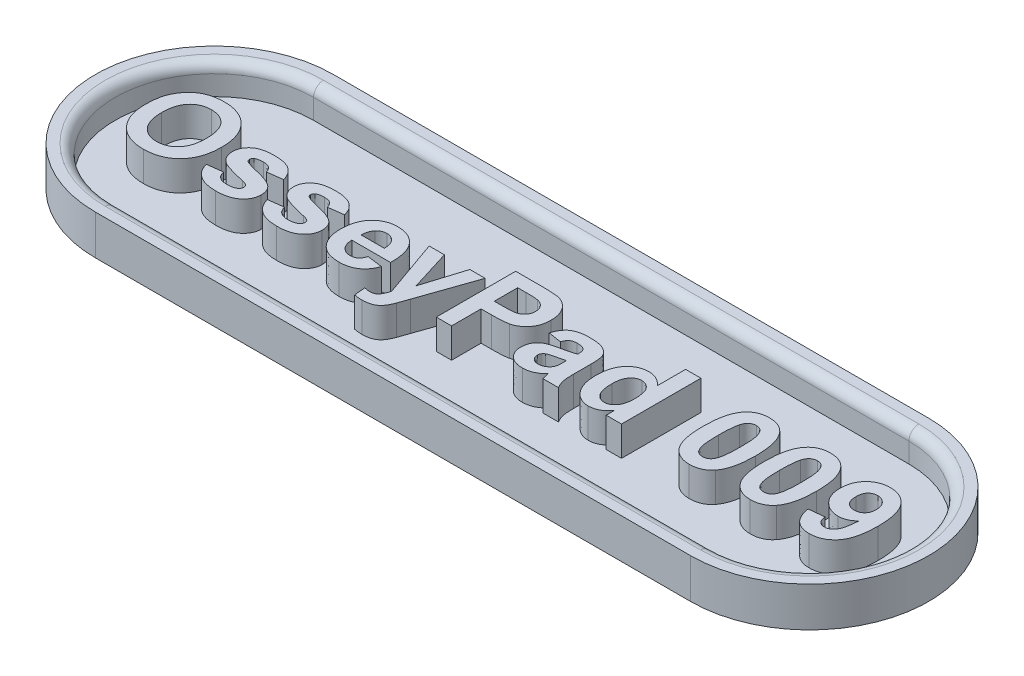
SolidWorks part; units mm, degrees
ref_plane "Front Plane" through (0, 0, 0) normal (0, 0, 1) x (1, 0, 0)
ref_plane "Top Plane" through (0, 0, 0) normal (0, 1, 0) x (1, 0, 0)
ref_plane "Right Plane" through (0, 0, 0) normal (1, 0, 0) x (0, 0, -1)
sketch "Sketch1" plane through (0, 0, 0) normal (0, 1, 0) x (1, 0, 0)
  line L0 (-15, 0) -> (15, 0) construction
  line L1 (-15, 6) -> (15, 6)
  line L2 (-15, -6) -> (15, -6)
  arc A0 (-15, 6) -> (-15, -6) centre (-15, 0) ccw
  arc A1 (15, -6) -> (15, 6) centre (15, 0) ccw
  point P2 (0, 0)
  dimension "D1" = 12
  dimension "D2" = 30
extrude "Boss-Extrude1" add sketch "Sketch1" along normal blind 2
sketch "Sketch2" plane through (0, 2, 0) normal (0, 1, 0) x (1, 0, 0)
  line L0 (-15, 0) -> (15, 0) construction
  line L1 (-15, 5) -> (15, 5)
  line L2 (-15, -5) -> (15, -5)
  arc A0 (-15, 5) -> (-15, -5) centre (-15, 0) ccw
  arc A1 (15, -5) -> (15, 5) centre (15, 0) ccw
  point P2 (0, 0)
  dimension "D1" = 30
  dimension "D2" = 10
extrude "Cut-Extrude1" cut sketch "Sketch2" against normal blind 1.5
sketch "Sketch3" plane through (0, 0.5, 0) normal (0, 1, 0) x (1, 0, 0)
  line L0 (-21, -1.995) -> (21, -1.995) construction
  line L1 (0, -8.7006) -> (0, 6.9821) construction
  line L3 (-15, -5) -> (15, -5) construction
  text T0 "OsseyPad 009" font "Arial" height 4
  dimension "D1" = 3.005
extrude "Boss-Extrude2" add sketch "Sketch3" along normal blind 1.5
fillet "Fillet1" radius 0.5 4 edges at (0, 2, -5) (20, 2, 0) (0, 2, 5) (-20, 2, 0)
